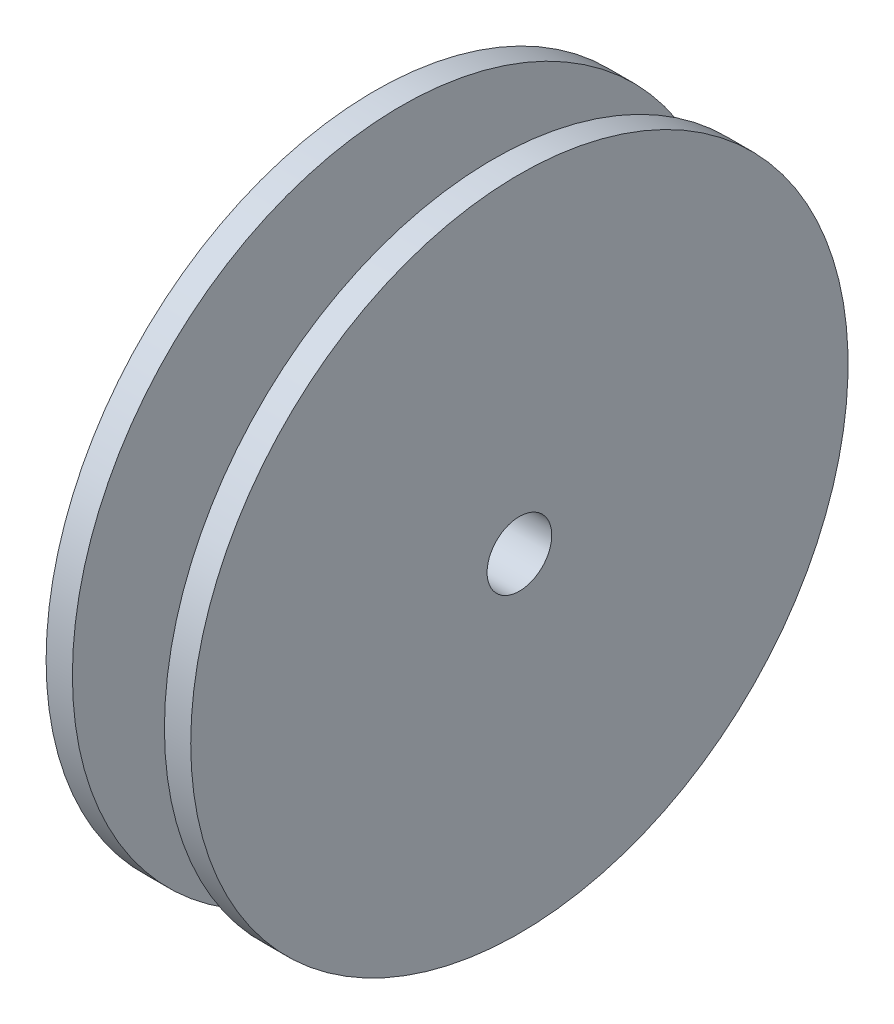
SolidWorks part; units mm, degrees
ref_plane "Front Plane" through (0, 0, 0) normal (0, 0, 1) x (1, 0, 0)
ref_plane "Top Plane" through (0, 0, 0) normal (0, 1, 0) x (1, 0, 0)
ref_plane "Right Plane" through (0, 0, 0) normal (1, 0, 0) x (0, 0, -1)
sketch "Sketch1" plane through (0, 0, 0) normal (0, 0, 1) x (1, 0, 0)
  line L0 (0, 0) -> (19.05, 0)
  line L1 (19.05, 0) -> (19.05, 31.75)
  line L2 (19.05, 31.75) -> (16.51, 31.75)
  line L3 (16.51, 31.75) -> (16.51, 19.05)
  line L4 (16.51, 19.05) -> (7.62, 19.05)
  line L5 (7.62, 19.05) -> (7.62, 31.75)
  line L6 (7.62, 31.75) -> (5.08, 31.75)
  line L7 (5.08, 31.75) -> (5.08, 6.35)
  line L8 (5.08, 6.35) -> (0, 6.35)
  line L9 (0, 6.35) -> (0, 0)
  dimension "D1" = 6.35
  dimension "D2" = 5.08
  dimension "D3" = 31.75
  dimension "D4" = 12.7
  dimension "D5" = 2.54
  dimension "D6" = 2.54
  dimension "D7" = 19.05
revolve "Revolve1" add sketch "Sketch1" angle 360 about L0
sketch "Sketch2" plane through (0, 0, 0) normal (-1, 0, 0) x (0, 0, 1)
  circle A0 centre (0, 0) radius 3.1242
  dimension "D1" = 6.2484
extrude "Cut-Extrude1" cut sketch "Sketch2" against normal through all
